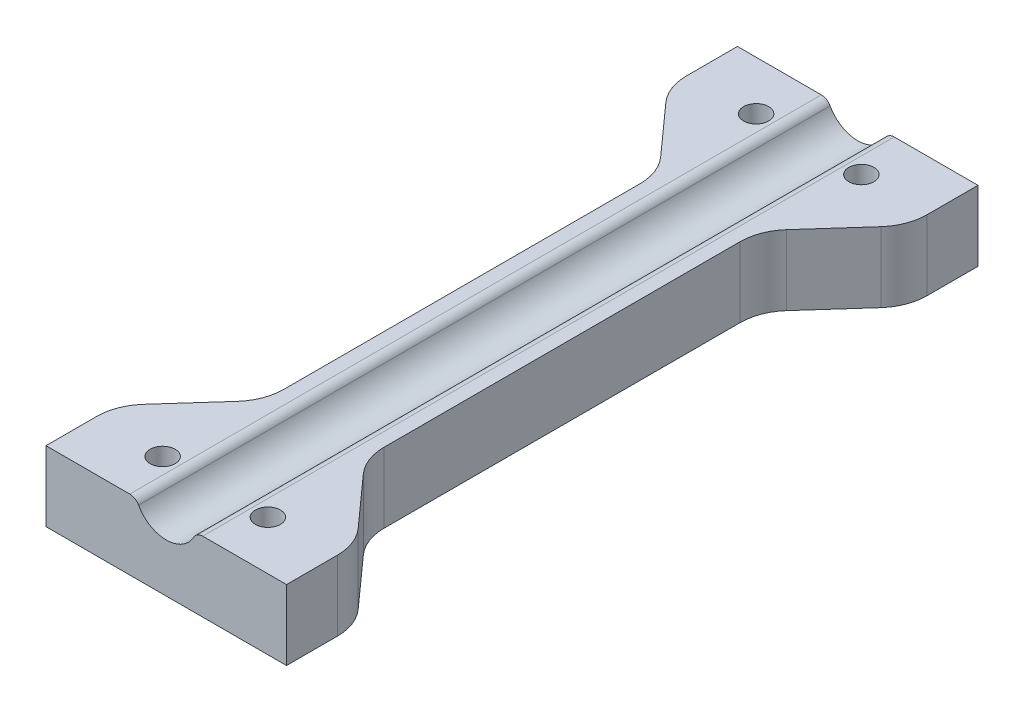
SolidWorks part; units mm, degrees
ref_plane "Front Plane" through (0, 0, 0) normal (0, 0, 1) x (1, 0, 0)
ref_plane "Top Plane" through (0, 0, 0) normal (0, 1, 0) x (1, 0, 0)
ref_plane "Right Plane" through (0, 0, 0) normal (1, 0, 0) x (0, 0, -1)
sketch "Sketch1" plane through (0, 0, 0) normal (0, 0, 1) x (1, 0, 0)
  line L0 (-12, -1) -> (-2.9871, -1)
  line L1 (-12, -1) -> (-12, -8)
  line L2 (-12, -8) -> (12, -8)
  line L3 (0, 10.6085) -> (0, -11.9541) construction
  line L4 (12, -1) -> (12, -8)
  line L5 (12, -1) -> (2.9871, -1)
  arc A0 (-2.9871, -1) -> (2.9871, -1) centre (0, 0) ccw
  point P10 (0, -8)
  dimension "D1" = 3.15
  dimension "D2" = 24
  dimension "D3" = 7
  dimension "D4" = 1
extrude "Boss-Extrude1" add sketch "Sketch1" along normal mid plane 69
fillet "Fillet1" radius 1 2 edges at (2.9871, -1, 0) (-2.9871, -1, 0)
sketch "Sketch2" plane through (0, -1, 0) normal (0, 1, 0) x (1, 0, 0)
  line L0 (-12, 27.5) -> (-5, 19.6866)
  line L1 (-5, 19.6866) -> (-5, -19.6866)
  line L2 (-19.2601, 0) -> (19.7706, 0) construction
  line L3 (0, 0) -> (0, 23.4021) construction
  line L4 (-12, 27.5) -> (-12, -27.5)
  line L5 (-12, -27.5) -> (-5, -19.6866)
  line L6 (12, -27.5) -> (5, -19.6866)
  line L7 (12, 27.5) -> (12, -27.5)
  line L8 (5, 19.6866) -> (5, -19.6866)
  line L9 (12, 27.5) -> (5, 19.6866)
  line L10 (-12, -34.5) -> (-12, 34.5) construction
  line L11 (-3.6363, 34.5) -> (-12, 34.5) construction
  point P3 (5, 0)
  point P10 (-12, 0)
  point P11 (-5, 0)
  point P12 (12, 0)
  point P19 (8, 24.108)
  dimension "D1" = 5
  dimension "D2" = 7
extrude "Cut-Extrude1" cut sketch "Sketch2" against normal through all
fillet "Fillet2" radius 5 8 edges at (-12, -4.5, 27.5) (-5, -4.5, 19.6866) (5, -4.5, 19.6866) (12, -4.5, 27.5) (-12, -4.5, -27.5) (-5, -4.5, -19.6866) (5, -4.5, -19.6866) (12, -4.5, -27.5)
sketch "Sketch3" plane through (0, -1, 0) normal (0, 1, 0) x (1, 0, 0)
  line L0 (-9.8386, 0) -> (14.5607, 0) construction
  line L1 (-5.25, 29.6102) -> (5.25, 29.6102) construction
  circle A0 centre (5.25, 29.6102) radius 1.25
  circle A1 centre (-5.25, 29.6102) radius 1.25
  circle A2 centre (-5.25, -29.6102) radius 1.25
  circle A3 centre (5.25, -29.6102) radius 1.25
  point P7 (0, 29.6102)
  dimension "D2" = 2.5
  dimension "D1" = 10.5
extrude "Cut-Extrude2" cut sketch "Sketch3" against normal through all
